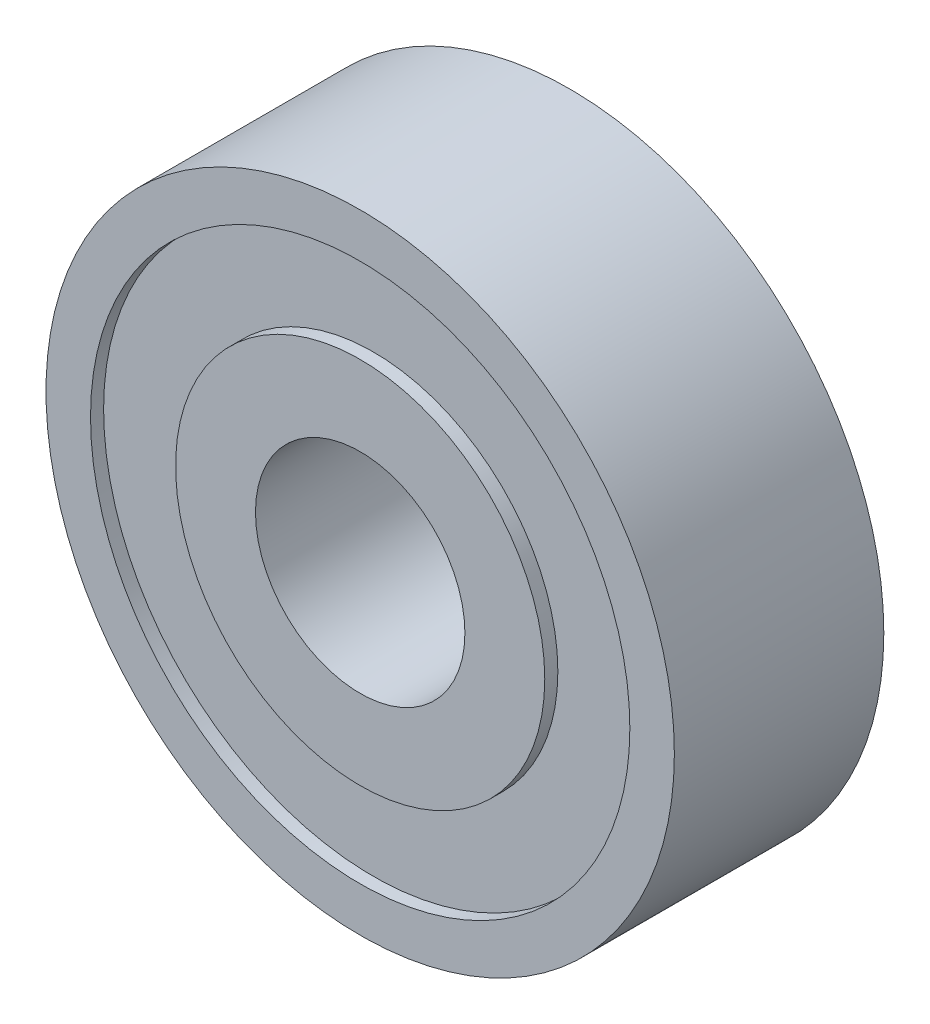
SolidWorks part; units mm, degrees
material "201 退火不鏽鋼 (SS)"
ref_plane "前基準面" through (0, 0, 0) normal (0, 0, 1) x (1, 0, 0)
ref_plane "上基準面" through (0, 0, 0) normal (0, 1, 0) x (1, 0, 0)
ref_plane "右基準面" through (0, 0, 0) normal (1, 0, 0) x (0, 0, -1)
sketch "草圖1" plane through (0, 0, 0) normal (0, 0, 1) x (1, 0, 0)
  circle A0 centre (0, 0) radius 12
  dimension "D1" = 24
extrude "填料-伸長1" add sketch "草圖1" along normal mid plane 8
sketch "草圖2" plane through (0, 0, 4) normal (0, 0, 1) x (1, 0, 0)
  circle A0 centre (0, 0) radius 4
  dimension "D1" = 8
extrude "除料-伸長1" cut sketch "草圖2" against normal through all
sketch "草圖3" plane through (0, 0, 4) normal (0, 0, 1) x (1, 0, 0)
  circle A0 centre (0, 0) radius 7.05
  circle A1 centre (0, 0) radius 10.3
  dimension "D1" = 20.6
  dimension "D2" = 14.1
extrude "除料-伸長2" cut sketch "草圖3" against normal blind 0.5
mirror "鏡射1" about plane through (0, 0, 0) normal (0, 0, 1) of "除料-伸長2"
